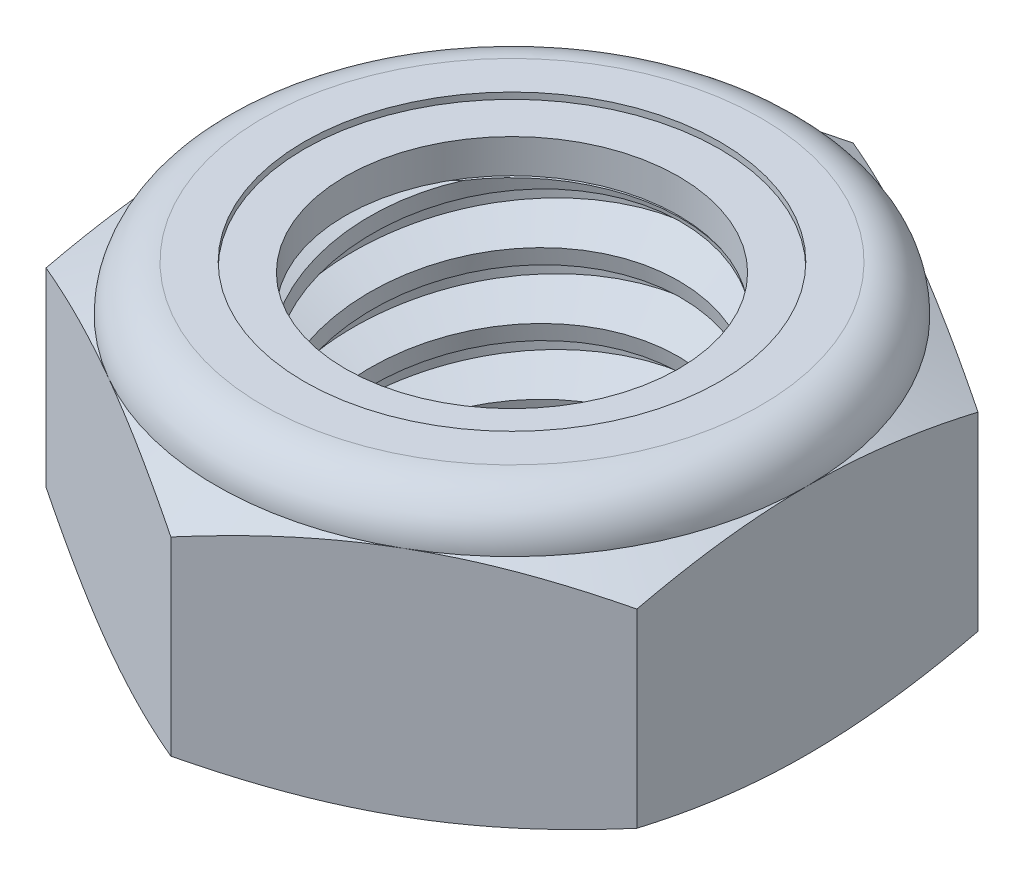
SolidWorks part; units mm, degrees
ref_plane "Front" through (0, 0, 0) normal (0, 0, 1) x (1, 0, 0)
ref_plane "Top" through (0, 0, 0) normal (0, 1, 0) x (1, 0, 0)
ref_plane "Right" through (0, 0, 0) normal (1, 0, 0) x (0, 0, -1)
sketch "Sketch1" plane through (0, 0, 0) normal (0, 1, 0) x (1, 0, 0)
  line L1 (0, 8.2489) -> (-7.1438, 4.1244)
  line L2 (-7.1438, 4.1244) -> (-7.1438, -4.1244)
  line L3 (-7.1438, -4.1244) -> (0, -8.2489)
  line L4 (0, -8.2489) -> (7.1437, -4.1244)
  line L5 (7.1437, -4.1244) -> (7.1437, 4.1244)
  line L6 (7.1437, 4.1244) -> (0, 8.2489)
  circle A0 centre (0, 0) radius 7.1438 construction
  dimension "Hex Flats" = 14.2875
extrude "Extrude1" add sketch "Sketch1" along normal blind 6.7469
sketch "Sketch2" plane through (0, 0, 0) normal (1, 0, 0) x (0, 0, -1)
  line L0 (-4.7625, 0) -> (-4.7625, 6.7469) construction
  line L1 (0, 0) -> (4.7625, 0)
  line L2 (0, 0) -> (0, 6.7469)
  line L3 (0, 6.7469) -> (4.7625, 6.7469)
  line L4 (4.7625, 0) -> (4.7625, 6.7469)
  line L5 (-4.1244, 6.7469) -> (4.1244, 6.7469) construction
  line L7 (0, -4.7625) -> (0, 0) construction
  dimension "Thread Dia" = 9.525
revolve "Revolve1" add sketch "Sketch2" angle 360 about L7
sketch "Sketch3" plane through (0, 0, 0) normal (1, 0, 0) x (0, 0, -1)
  line L0 (4.7625, 6.7469) -> (-4.7625, 6.7469) construction
  line L1 (-4.7625, 6.7469) -> (-4.7625, 5.1594) construction
  line L2 (-4.7625, 5.1594) -> (4.7625, 6.7469) construction
  line L3 (4.7625, 6.7469) -> (4.7951, 6.5511) construction
  line L4 (4.7951, 6.5511) -> (5.0235, 5.181)
  line L5 (5.0235, 5.181) -> (4.0944, 5.5291)
  line L6 (4.0944, 5.5291) -> (4.0291, 5.9205)
  line L7 (4.0291, 5.9205) -> (4.7951, 6.5511)
  line L8 (4.0617, 5.7248) -> (4.9093, 5.8661) construction
  line L9 (4.7625, 6.7469) -> (4.7625, 5.8416) construction
  line L10 (4.7625, 5.8416) -> (-4.7625, 4.2541) construction
  line L11 (-4.7625, 4.2541) -> (-4.7625, 5.1594) construction
  line L12 (-0.2832, 6.7469) -> (0.2832, 3.3488) construction
  line L13 (-4.7625, 0) -> (-4.7625, 6.7469) construction
  line L14 (0, 6.7469) -> (4.7625, 6.7469) construction
  line L15 (4.7625, 0) -> (4.7625, 6.7469) construction
  point P13 (0, 5.0478)
  dimension "D1" = 0.1984
  dimension "D2" = 0.3969
  dimension "Thread Pitch" = 1.5875
  dimension "D4" = 60
  dimension "D5" = 1.5875
revolve "Cut-Revolve1" cut sketch "Sketch3" angle 360 about L12
pattern_linear "LPattern1" count 4 spacing 1.5875 along (0, -1, 0) count 2 spacing 1.5875 along (0, 1, 0) of "Cut-Revolve1"
sketch "Sketch4" plane through (0, 0, 0) normal (1, 0, 0) x (0, 0, -1)
  line L0 (0, 6.7469) -> (4.7625, 6.7469)
  line L1 (4.7625, 6.7469) -> (4.0291, 6.4049)
  line L2 (4.0291, 6.4049) -> (4.0291, 0.342)
  line L3 (4.0291, 0.342) -> (4.7625, 0)
  line L4 (4.7625, 0) -> (0, 0)
  line L5 (0, 0) -> (0, 6.7469)
  line L6 (4.7625, 0) -> (4.7625, 6.7469) construction
  line L7 (0, 6.7469) -> (4.7625, 6.7469) construction
  line L8 (0, 0) -> (4.7625, 0) construction
  line L9 (0, 0) -> (0, 6.7469) construction
  line L10 (0, 6.7469) -> (0, 7.5561) construction
  dimension "D1" = 25
revolve "Cut-Revolve2" cut sketch "Sketch4" angle 360 about L10
combine bodies "Combine1" operation type subtract main body 112 bodies to subtract 111
sketch "Sketch5" plane through (0, 0, 0) normal (1, 0, 0) x (0, 0, -1)
  line L0 (0, 0) -> (7.1438, 0)
  line L1 (7.1438, 0) -> (8.2489, 0.5153)
  line L2 (8.2489, 0.5153) -> (8.2489, 5.1071)
  line L3 (8.2489, 5.1071) -> (7.1438, 5.6224)
  line L4 (6.0193, 6.7469) -> (6.0193, 8.0169)
  line L5 (6.0193, 8.0169) -> (9.5189, 8.0169)
  line L6 (9.5189, 8.0169) -> (9.5189, -1.27)
  line L7 (9.5189, -1.27) -> (0, -1.27)
  line L8 (0, -1.27) -> (0, 0)
  line L9 (7.1438, 5.6224) -> (7.1438, 0) construction
  line L10 (0, 0) -> (4.7625, 0) construction
  line L13 (8.2489, 2.8112) -> (9.5189, 2.8112) construction
  line L14 (8.2489, 6.7469) -> (8.2489, 0) construction
  line L15 (0, 0) -> (0, 8.0169) construction
  line L20 (0, 8.0169) -> (6.0193, 8.0169) construction
  line L22 (0, 6.7469) -> (4.7625, 6.7469) construction
  arc A0 (7.1438, 5.6224) -> (6.0193, 6.7469) centre (6.0193, 5.6224) ccw
  dimension "D1" = 25
  dimension "D2" = 1.27
  dimension "D3" = 6.7469
  dimension "D4" = 1.1245
revolve "Cut-Revolve3" cut sketch "Sketch5" angle 360 about L15
sketch "Sketch6" plane through (0, 0, 0) normal (1, 0, 0) x (0, 0, -1)
  line L0 (0, 5.6224) -> (6.9914, 5.6224)
  line L1 (6.0193, 6.5945) -> (5.0242, 6.5945)
  line L2 (0, 8.0169) -> (0, 5.6224)
  line L3 (5.0242, 8.0169) -> (0, 8.0169)
  line L4 (0, 8.0169) -> (6.0193, 8.0169) construction
  line L5 (0, 0) -> (0, 8.0169) construction
  line L6 (0, 8.0169) -> (0, 44.323) construction
  line L7 (5.0242, 6.5945) -> (5.0242, 8.0169)
  line L8 (6.0193, 6.7469) -> (6.0193, 6.5945) construction
  line L9 (5.0242, 6.5945) -> (4.0291, 6.5945) construction
  line L10 (4.0291, 6.5945) -> (4.0291, 6.4049) construction
  arc A0 (6.9914, 5.6224) -> (6.0193, 6.5945) centre (6.0193, 5.6224) ccw
  arc A1 (7.1438, 5.6224) -> (6.0193, 6.7469) centre (6.0193, 5.6224) ccw construction
  dimension "D1" = 0.1524
revolve "Cut-Revolve4" cut sketch "Sketch6" angle 360 about L6
sketch "Sketch7" plane through (0, 0, 0) normal (1, 0, 0) x (0, 0, -1)
  line L0 (4.0291, 5.6986) -> (6.9119, 5.6986)
  line L1 (6.0193, 6.5183) -> (4.0291, 6.5183)
  line L2 (4.0291, 6.5183) -> (4.0291, 5.6986)
  line L3 (4.0291, 5.6986) -> (0, 5.6986) construction
  line L4 (0, 5.6986) -> (0, 6.5183) construction
  line L5 (0, 6.5183) -> (4.0291, 6.5183) construction
  line L6 (4.0291, 5.6986) -> (4.0291, 5.6224) construction
  line L7 (0, 5.6224) -> (6.9914, 5.6224) construction
  line L8 (6.0193, 6.5183) -> (6.0193, 6.5945) construction
  arc A0 (6.9119, 5.6986) -> (6.0193, 6.5183) centre (6.0193, 5.6224) ccw
  arc A2 (6.9914, 5.6224) -> (6.0193, 6.5945) centre (6.0193, 5.6224) ccw construction
  dimension "D1" = 0.0762
revolve "Revolve2" add sketch "Sketch7" angle 360 about L4
equation "\"D1@Sketch3\"=\"Thread Pitch@Sketch3\"/8"
equation "\"D2@Sketch3\"=\"Thread Pitch@Sketch3\"/4"
equation "\"D5@Sketch3\"=\"Thread Pitch@Sketch3\""
equation "\"D4@LPattern1\"=\"Thread Pitch@Sketch3\""
equation "\"D3@LPattern1\"=\"Thread Pitch@Sketch3\""
equation "\"D1@LPattern1\"=\"Height@Extrude1\"/\"Thread Pitch@Sketch3\""
equation "\"D4@Sketch5\"=\"Height@Extrude1\"/6"
